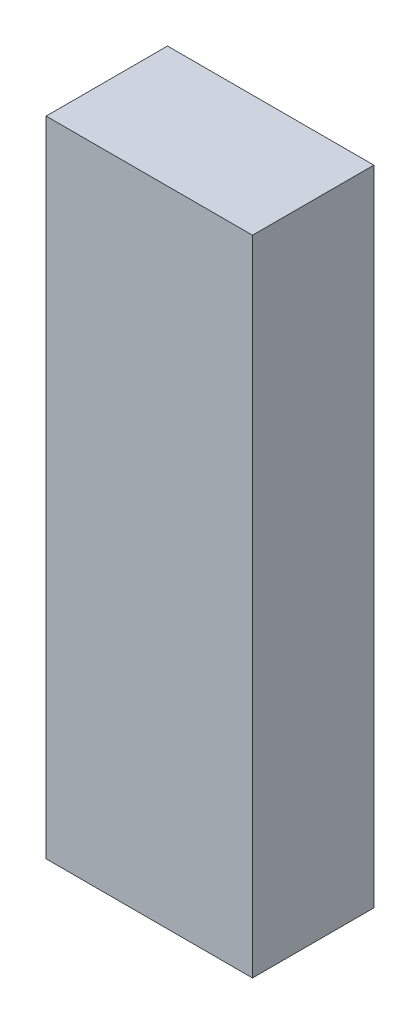
SolidWorks part; units mm, degrees
ref_plane "Front" through (0, 0, 0) normal (0, 0, 1) x (1, 0, 0)
ref_plane "Top" through (0, 0, 0) normal (0, 1, 0) x (1, 0, 0)
ref_plane "Right" through (0, 0, 0) normal (1, 0, 0) x (0, 0, -1)
sketch "Sketch1" plane through (0, 0, 0) normal (0, 0, 1) x (1, 0, 0)
  line L0 (0, 0) -> (34, 0)
  line L1 (34, 0) -> (34, 106)
  line L2 (34, 106) -> (0, 106)
  line L3 (0, 106) -> (0, 0)
extrude "Boss-Extrude1" add sketch "Sketch1" along normal blind 20
